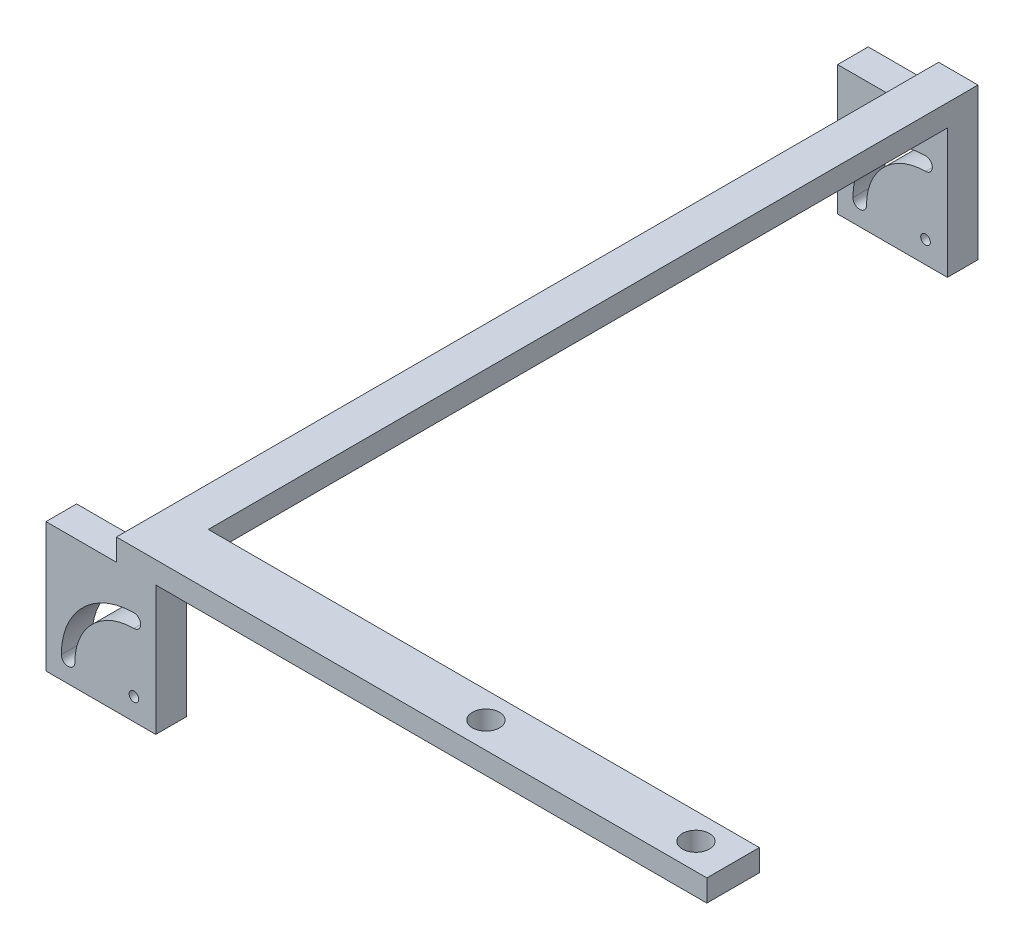
SolidWorks part; units mm, degrees
ref_plane "Front Plane" through (0, 0, 0) normal (0, 0, 1) x (1, 0, 0)
ref_plane "Top Plane" through (0, 0, 0) normal (0, 1, 0) x (1, 0, 0)
ref_plane "Right Plane" through (0, 0, 0) normal (1, 0, 0) x (0, 0, -1)
sketch "Sketch24" plane through (0, 0, 0) normal (0, 0, 1) x (1, 0, 0)
  line L1 (0, 0) -> (25.1, 0)
  line L2 (0, 0) -> (0, 29.6)
  line L3 (0, 29.6) -> (25.1, 29.6)
  line L4 (25.1, 0) -> (25.1, 29.6)
extrude "Boss-Extrude8" add sketch "Sketch24" along normal blind 7
sketch "Sketch26" plane through (0, 29.6, 0) normal (0, 1, 0) x (1, 0, 0)
  line L1 (25.1, -7) -> (16.1, -7)
  line L2 (25.1, -7) -> (25.1, 0)
  line L3 (25.1, 0) -> (16.1, 0)
  line L4 (16.1, -7) -> (16.1, 0)
extrude "Boss-Extrude9" add sketch "Sketch26" along normal blind 5
sketch "Sketch27" plane through (0, 0, 0) normal (0, 0, -1) x (-1, 0, 0)
  line L1 (-25.1, 34.6) -> (-16.1, 34.6)
  line L2 (-25.1, 34.6) -> (-25.1, 29.6)
  line L3 (-25.1, 29.6) -> (-16.1, 29.6)
  line L4 (-16.1, 34.6) -> (-16.1, 29.6)
extrude "Boss-Extrude10" add sketch "Sketch27" along normal blind 174
sketch "Sketch28" plane through (0, 0, -174) normal (0, 0, -1) x (-1, 0, 0)
  line L1 (-25.1, 34.6) -> (0, 34.6)
  line L2 (-25.1, 34.6) -> (-25.1, 0)
  line L3 (-25.1, 0) -> (0, 0)
  line L4 (0, 34.6) -> (0, 0)
extrude "Boss-Extrude11" add sketch "Sketch28" along normal blind 7
sketch "Sketch29" plane through (0, 0, -174) normal (0, 0, 1) x (1, 0, 0)
  line L1 (0, 34.6) -> (16.1, 34.6)
  line L2 (0, 34.6) -> (0, 29.6)
  line L3 (0, 29.6) -> (16.1, 29.6)
  line L4 (16.1, 34.6) -> (16.1, 29.6)
extrude "Cut-Extrude8" cut sketch "Sketch29" against normal blind 15
sketch "Sketch32" plane through (0, 0, -181) normal (0, 0, -1) x (-1, 0, 0)
  arc A0 (-6.6, 5) -> (-20.1, 18.5) centre (-20.1, 5) ccw
  arc A1 (-3.5, 5) -> (-20.1, 21.6) centre (-20.1, 5) ccw
  arc A2 (-20.1, 21.6) -> (-20.1, 18.5) centre (-20.1, 20.05) ccw
  arc A3 (-3.5, 5) -> (-6.6, 5) centre (-5.05, 5) cw
  circle A4 centre (-20.1, 5) radius 1.1
extrude "Cut-Extrude11" cut sketch "Sketch32" against normal blind 29
sketch "Sketch33" plane through (0, 0, 7) normal (0, 0, 1) x (1, 0, 0)
  arc A0 (6.6, 5) -> (20.1, 18.5) centre (20.1, 5) cw
  arc A1 (3.5, 5) -> (20.1, 21.6) centre (20.1, 5) cw
  arc A2 (20.1, 21.6) -> (20.1, 18.5) centre (20.1, 20.05) cw
  arc A3 (6.6, 5) -> (3.5, 5) centre (5.05, 5) cw
  circle A4 centre (20.1, 5) radius 1.1
extrude "Cut-Extrude13" cut sketch "Sketch33" against normal blind 21
sketch "Sketch35" plane through (25.1, 0, 0) normal (1, 0, 0) x (0, 0, -1)
  line L0 (174, 29.6) -> (0, 29.6) construction
  line L1 (-7, 34.6) -> (5, 34.6)
  line L2 (-7, 34.6) -> (-7, 29.6)
  line L3 (-7, 29.6) -> (5, 29.6)
  line L4 (5, 34.6) -> (5, 29.6)
extrude "Boss-Extrude12" add sketch "Sketch35" along normal blind 126
sketch "Sketch38" plane through (0, 34.6, 0) normal (0, 1, 0) x (1, 0, 0)
  circle A0 centre (142.6, -1) radius 3.1
  circle A1 centre (94.6, -1) radius 3.1
extrude "Cut-Extrude14" cut sketch "Sketch38" against normal blind 126
